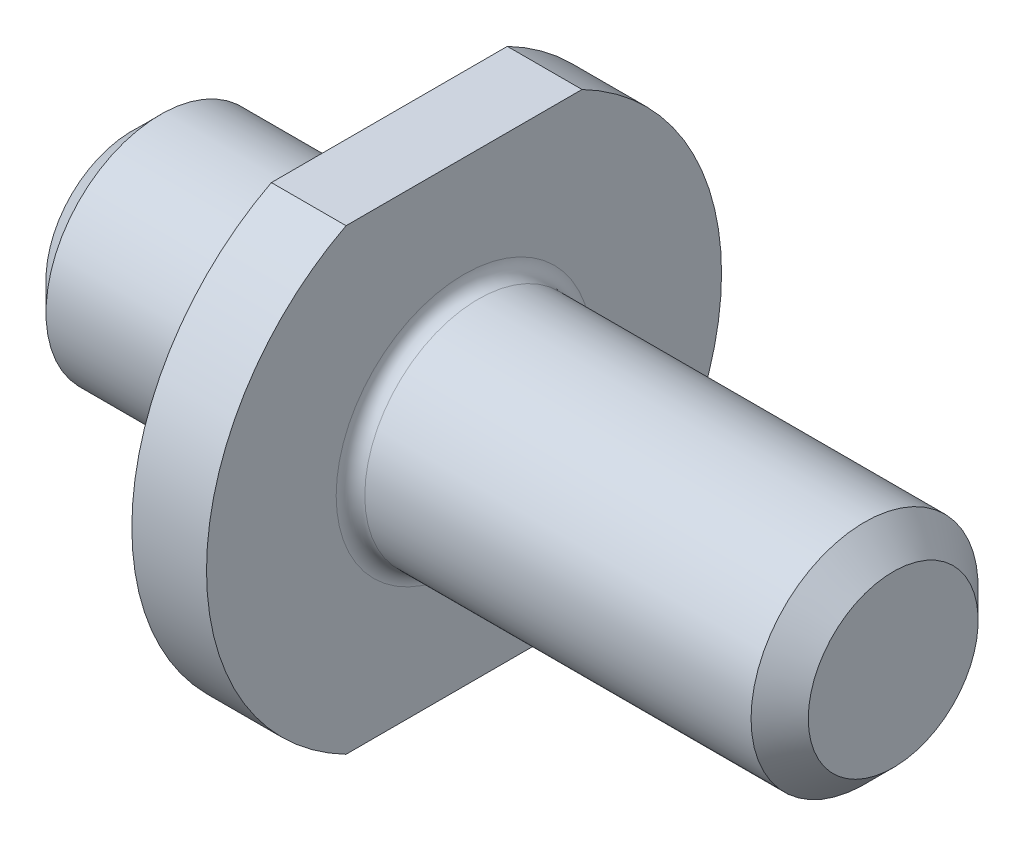
SolidWorks part; units mm, degrees
ref_plane "Front Plane" through (0, 0, 0) normal (0, 0, 1) x (1, 0, 0)
ref_plane "Top Plane" through (0, 0, 0) normal (0, 1, 0) x (1, 0, 0)
ref_plane "Right Plane" through (0, 0, 0) normal (1, 0, 0) x (0, 0, -1)
sketch "Sketch1" plane through (0, 0, 0) normal (0, 0, 1) x (1, 0, 0)
  line L0 (0, 4) -> (0, 9)
  line L1 (0, 9) -> (2.61, 9)
  line L2 (2.61, 9) -> (2.61, 3.9688)
  line L3 (2.61, 3.9688) -> (17.61, 3.9688)
  line L4 (17.61, 3.9688) -> (17.61, 0)
  line L5 (17.61, 0) -> (-9, 0)
  line L6 (-9, 0) -> (-9, 4)
  line L7 (-9, 4) -> (0, 4)
  line L8 (-38.174, 0) -> (38.174, 0) construction
  dimension "D1" = 2.61
  dimension "D2" = 7.9375
  dimension "D3" = 8
  dimension "D4" = 18
  dimension "D5" = 9
  dimension "D6" = 15
revolve "Revolve1" add sketch "Sketch1" angle 360 about L8
cosmetic thread "Cosmetic Thread1" parameters "D1"=9, "D2"=6.6777
chamfer "Chamfer1" distance 1 angle 45 2 edges at (17.61, 0, 3.9688) (-9, 0, 4)
fillet "Fillet1" radius 0.5 2 edges at (2.61, 0, 3.9688) (0, 0, 4)
sketch "Sketch2" plane through (0, 0, 0) normal (1, 0, 0) x (0, 0, -1)
  line L1 (-13.378, -8) -> (13.378, -8)
  line L2 (-13.378, -8) -> (-13.378, 8)
  line L3 (-13.378, 8) -> (13.378, 8)
  line L4 (13.378, -8) -> (13.378, 8)
  line L5 (-13.378, -8) -> (13.378, 8) construction
  line L6 (-13.378, 8) -> (13.378, -8) construction
  point P0 (0, 0)
  dimension "D1" = 16
extrude "Cut-Extrude1" cut sketch "Sketch2" along normal through all and the other way through all flip side to cut
